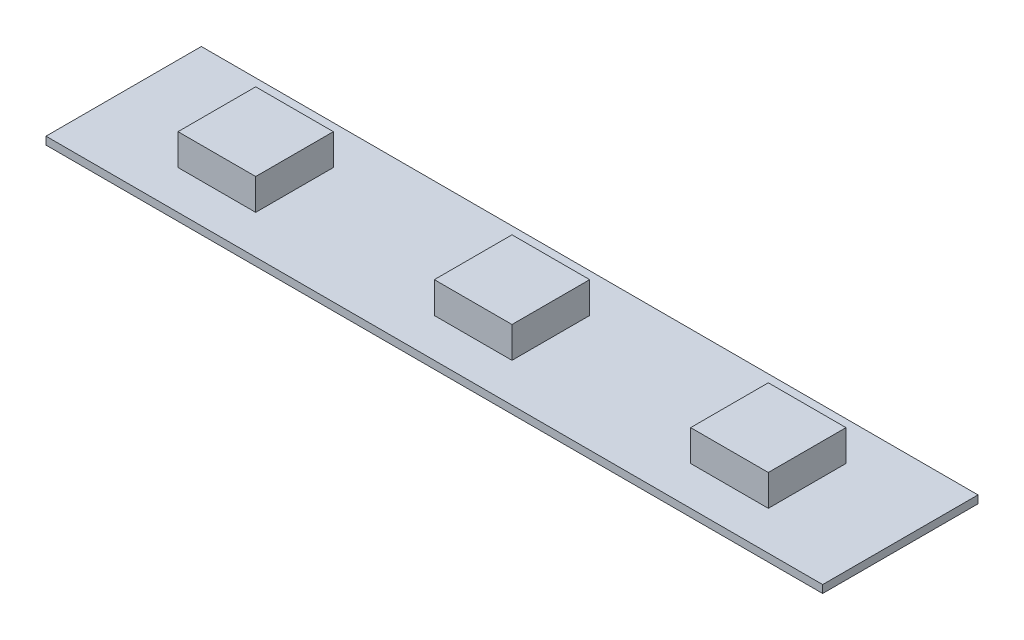
SolidWorks part; units mm, degrees
ref_plane "Front Plane" through (0, 0, 0) normal (0, 0, 1) x (1, 0, 0)
ref_plane "Top Plane" through (0, 0, 0) normal (0, 1, 0) x (1, 0, 0)
ref_plane "Right Plane" through (0, 0, 0) normal (1, 0, 0) x (0, 0, -1)
sketch "Sketch1" plane through (0, 0, 0) normal (0, 1, 0) x (1, 0, 0)
  line L1 (-25, -5) -> (25, -5)
  line L2 (-25, -5) -> (-25, 5)
  line L3 (-25, 5) -> (25, 5)
  line L4 (25, -5) -> (25, 5)
  line L5 (-25, -5) -> (25, 5) construction
  line L6 (-25, 5) -> (25, -5) construction
  point P0 (0, 0)
  dimension "D1" = 50
  dimension "D2" = 10
extrude "Boss-Extrude1" add sketch "Sketch1" along normal blind 0.5
sketch "Sketch11" plane through (0, 0.5, 0) normal (0, 1, 0) x (1, 0, 0)
  line L0 (0, 0) -> (-16.5006, 0)
  line L1 (0, 0) -> (16.5006, 0)
sketch "Sketch12" plane through (0, 0.5, 0) normal (0, 1, 0) x (1, 0, 0)
  line L1 (-19.0006, -2.5) -> (-14.0006, -2.5)
  line L2 (-19.0006, -2.5) -> (-19.0006, 2.5)
  line L3 (-19.0006, 2.5) -> (-14.0006, 2.5)
  line L4 (-14.0006, -2.5) -> (-14.0006, 2.5)
  line L5 (-19.0006, -2.5) -> (-14.0006, 2.5) construction
  line L6 (-19.0006, 2.5) -> (-14.0006, -2.5) construction
  point P0 (-16.5006, 0)
  dimension "D1" = 5
  dimension "D2" = 5
extrude "Boss-Extrude8" add sketch "Sketch12" along normal blind 2
sketch "Sketch13" plane through (0, 0.5, 0) normal (0, 1, 0) x (1, 0, 0)
  line L1 (-2.5, -2.5) -> (2.5, -2.5)
  line L2 (-2.5, -2.5) -> (-2.5, 2.5)
  line L3 (-2.5, 2.5) -> (2.5, 2.5)
  line L4 (2.5, -2.5) -> (2.5, 2.5)
  line L5 (-2.5, -2.5) -> (2.5, 2.5) construction
  line L6 (-2.5, 2.5) -> (2.5, -2.5) construction
  point P0 (0, 0)
  dimension "D1" = 5
extrude "Boss-Extrude9" add sketch "Sketch13" along normal blind 2
sketch "Sketch14" plane through (0, 0.5, 0) normal (0, 1, 0) x (1, 0, 0)
  line L1 (19.0006, -2.5) -> (14.0006, -2.5)
  line L2 (19.0006, -2.5) -> (19.0006, 2.5)
  line L3 (19.0006, 2.5) -> (14.0006, 2.5)
  line L4 (14.0006, -2.5) -> (14.0006, 2.5)
  line L5 (19.0006, -2.5) -> (14.0006, 2.5) construction
  line L6 (19.0006, 2.5) -> (14.0006, -2.5) construction
  point P0 (16.5006, 0)
  dimension "D1" = 5
extrude "Boss-Extrude10" add sketch "Sketch14" along normal blind 2
